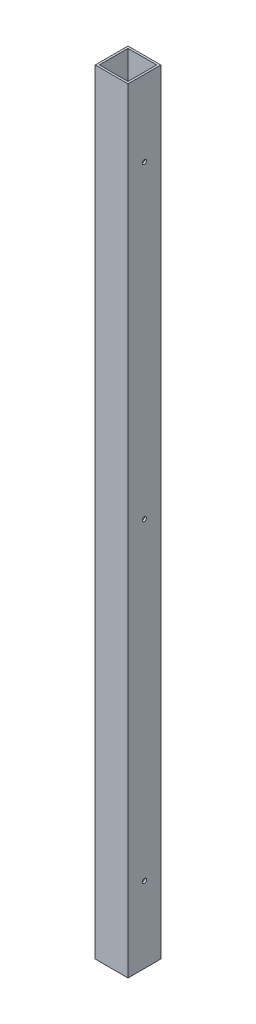
SolidWorks part; units mm, degrees
material "6061 Alloy"
ref_plane "Front Plane" through (0, 0, 0) normal (0, 0, 1) x (1, 0, 0)
ref_plane "Top Plane" through (0, 0, 0) normal (0, 1, 0) x (1, 0, 0)
ref_plane "Right Plane" through (0, 0, 0) normal (1, 0, 0) x (0, 0, -1)
sketch "Sketch1" plane through (0, 0, 0) normal (0, 1, 0) x (1, 0, 0)
  line L0 (22.225, -22.225) -> (22.225, 22.225)
  line L1 (25.4, -25.4) -> (-25.4, -25.4)
  line L2 (25.4, -25.4) -> (25.4, 25.4)
  line L3 (25.4, 25.4) -> (-25.4, 25.4)
  line L4 (-25.4, -25.4) -> (-25.4, 25.4)
  line L5 (25.4, -25.4) -> (-25.4, 25.4) construction
  line L6 (25.4, 25.4) -> (-25.4, -25.4) construction
  line L7 (22.225, 22.225) -> (-22.225, 22.225)
  line L8 (-22.225, -22.225) -> (-22.225, 22.225)
  line L9 (22.225, -22.225) -> (-22.225, -22.225)
  point P0 (0, 0)
  dimension "D1" = 50.8
  dimension "D2" = 50.8
  dimension "D3" = 3.175
extrude "Boss-Extrude1" add sketch "Sketch1" along normal blind 1200.15
sketch "Sketch2" plane through (25.4, 0, 0) normal (1, 0, 0) x (0, 0, -1)
  line L0 (-25.4, 1200.15) -> (25.4, 1200.15) construction
  line L2 (-25.4, 0) -> (25.4, 0) construction
  line L5 (-25.4, 1200.15) -> (-25.4, 0) construction
  line L6 (25.4, 600.075) -> (-25.4, 600.075) construction
  line L7 (25.4, 1200.15) -> (25.4, 0) construction
  circle A0 centre (0, 603.25) radius 3.302
  circle A1 centre (0, 117.602) radius 3.302
  circle A3 centre (0, 1082.548) radius 3.302
  dimension "D1" = 6.604
  dimension "D2" = 6.604
  dimension "D3" = 117.602
  dimension "D4" = 25.4
  dimension "D5" = 117.602
extrude "Cut-Extrude1" cut sketch "Sketch2" against normal blind 50.8
